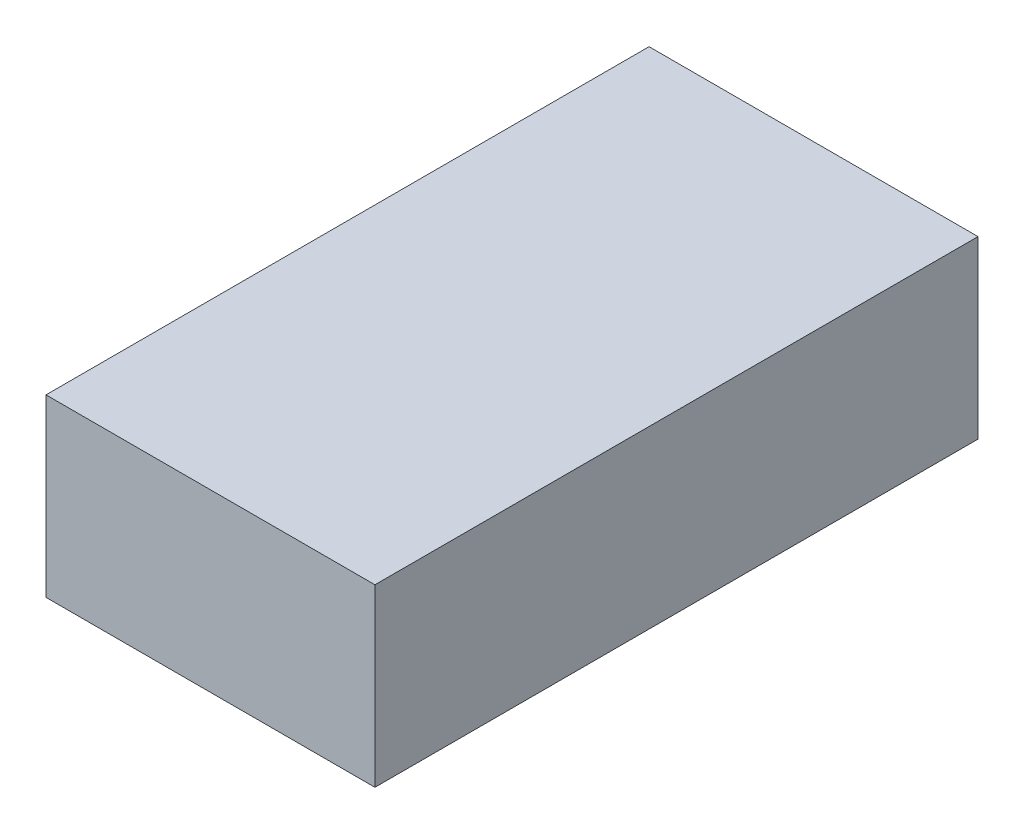
SolidWorks part; units mm, degrees
material "Default"
ref_plane "Top" through (0, 0, 0) normal (0, 0, 1) x (1, 0, 0)
ref_plane "Right" through (0, 0, 0) normal (0, 1, 0) x (1, 0, 0)
ref_plane "Front" through (0, 0, 0) normal (1, 0, 0) x (0, 0, -1)
sketch "Sketch1" plane through (0, 0, 0) normal (0, 1, 0) x (1, 0, 0)
  line L1 (32.8087, 20.9048) -> (62.8087, 20.9048)
  line L2 (32.8087, 20.9048) -> (32.8087, -34.0952)
  line L3 (32.8087, -34.0952) -> (62.8087, -34.0952)
  line L4 (62.8087, 20.9048) -> (62.8087, -34.0952)
  dimension "D1" = 55
  dimension "D2" = 30
extrude "Boss-Extrude1" add sketch "Sketch1" along normal blind 16
